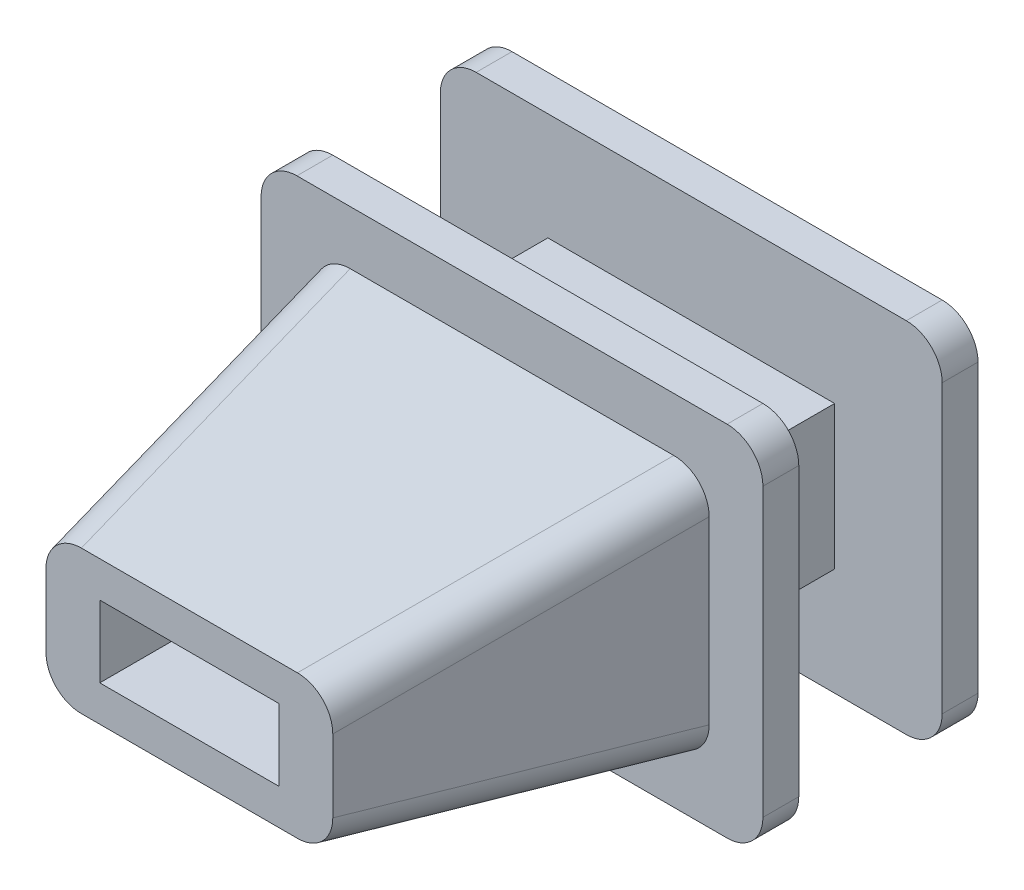
SolidWorks part; units mm, degrees
material "ABS"
ref_plane "Plan1" through (0, 0, 0) normal (0, 0, 1) x (1, 0, 0)
ref_plane "Plan2" through (0, 0, 0) normal (0, 1, 0) x (1, 0, 0)
ref_plane "Plan3" through (0, 0, 0) normal (1, 0, 0) x (0, 0, -1)
sketch "Esquisse1" plane through (0, 0, 0) normal (0, 0, 1) x (1, 0, 0)
  line L1 (-2, 1) -> (2, 1)
  line L2 (-2, 1) -> (-2, -1)
  line L3 (-2, -1) -> (2, -1)
  line L4 (2, 1) -> (2, -1)
  dimension "D1" = 4
  dimension "D2" = 2
  dimension "D3" = 2
  dimension "D4" = 1
extrude "Base-Extrusion" add sketch "Esquisse1" along normal blind 2
sketch "Esquisse2" plane through (0, 0, 0) normal (0, 0, -1) x (-1, 0, 0)
  line L1 (-3, 2.5) -> (3, 2.5)
  line L2 (-3.5, 2) -> (-3.5, -2)
  line L3 (-3, -2.5) -> (3, -2.5)
  line L4 (3.5, 2) -> (3.5, -2)
  arc A0 (3, -2.5) -> (3.5, -2) centre (3, -2) ccw
  arc A1 (3, 2.5) -> (3.5, 2) centre (3, 2) cw
  arc A2 (-3.5, 2) -> (-3, 2.5) centre (-3, 2) cw
  arc A3 (-3, -2.5) -> (-3.5, -2) centre (-3, -2) cw
  point P7 (3.5, -2.5)
  point P12 (-3.5, 2.5)
  point P15 (-3.5, -2.5)
  dimension "D5" = 0.5
  dimension "D1" = 5
  dimension "D2" = 7
  dimension "D3" = 3.5
  dimension "D4" = 2.5
extrude "Boss.-Extru.1" add sketch "Esquisse2" along normal blind 0.5
sketch "Esquisse3" plane through (0, 0, 2) normal (0, 0, 1) x (1, 0, 0)
  line L4 (-3, -2.5) -> (3, -2.5)
  line L5 (3.5, -2) -> (3.5, 2)
  line L6 (3, 2.5) -> (-3, 2.5)
  line L7 (-3.5, 2) -> (-3.5, -2)
  line L8 (-3, -2.5) -> (3, -2.5)
  line L9 (3.5, -2) -> (3.5, 2)
  line L10 (3, 2.5) -> (-3, 2.5)
  line L11 (-3.5, 2) -> (-3.5, -2)
  arc A4 (-3.5, -2) -> (-3, -2.5) centre (-3, -2) ccw
  arc A5 (3, -2.5) -> (3.5, -2) centre (3, -2) ccw
  arc A6 (3.5, 2) -> (3, 2.5) centre (3, 2) ccw
  arc A7 (-3, 2.5) -> (-3.5, 2) centre (-3, 2) ccw
  arc A8 (-3.5, -2) -> (-3, -2.5) centre (-3, -2) ccw
  arc A9 (3, -2.5) -> (3.5, -2) centre (3, -2) ccw
  arc A10 (3.5, 2) -> (3, 2.5) centre (3, 2) ccw
  arc A11 (-3, 2.5) -> (-3.5, 2) centre (-3, 2) ccw
  dimension "D1" = 0
extrude "Boss.-Extru.2" add sketch "Esquisse3" along normal blind 0.5
sketch "Esquisse4" plane through (0, 0, 2.5) normal (0, 0, 1) x (1, 0, 0)
  line L1 (-2.75, 1.75) -> (2.75, 1.75)
  line L2 (-2.75, 1.75) -> (-2.75, -1.75)
  line L3 (-2.75, -1.75) -> (2.75, -1.75)
  line L4 (2.75, 1.75) -> (2.75, -1.75)
  dimension "D1" = 5.5
  dimension "D2" = 3.5
  dimension "D3" = 2.75
  dimension "D4" = 1.75
ref_plane "Plan4" through (0, 0, 7) normal (0, 0, 1) x (1, 0, 0)
sketch "Esquisse5" plane through (0, 0, 7) normal (0, 0, 1) x (1, 0, 0)
  line L4 (2, 1) -> (-2, 1)
  line L5 (2, -1) -> (2, 1)
  line L6 (-2, -1) -> (2, -1)
  line L7 (-2, 1) -> (-2, -1)
  line L8 (2, 1) -> (-2, 1)
  line L9 (2, -1) -> (2, 1)
  line L10 (-2, -1) -> (2, -1)
  line L11 (-2, 1) -> (-2, -1)
  dimension "D1" = 0
loft "Boss.-Lissage1" add profiles "Esquisse4", "Esquisse5"
fillet "Congé1" radius 0.5 4 edges at (-2.375, 1.375, 4.75) (2.375, 1.375, 4.75) (-2.375, -1.375, 4.75) (2.375, -1.375, 4.75)
sketch "Esquisse6" plane through (0, 0, 7) normal (0, 0, 1) x (1, 0, 0)
  line L1 (-1.25, 0.5) -> (1.25, 0.5)
  line L2 (-1.25, 0.5) -> (-1.25, -0.5)
  line L3 (-1.25, -0.5) -> (1.25, -0.5)
  line L4 (1.25, 0.5) -> (1.25, -0.5)
  dimension "D1" = 1
  dimension "D2" = 2.5
  dimension "D3" = 0.5
  dimension "D4" = 1.25
extrude "Enlèv. mat.-Extru.1" cut sketch "Esquisse6" against normal through all
